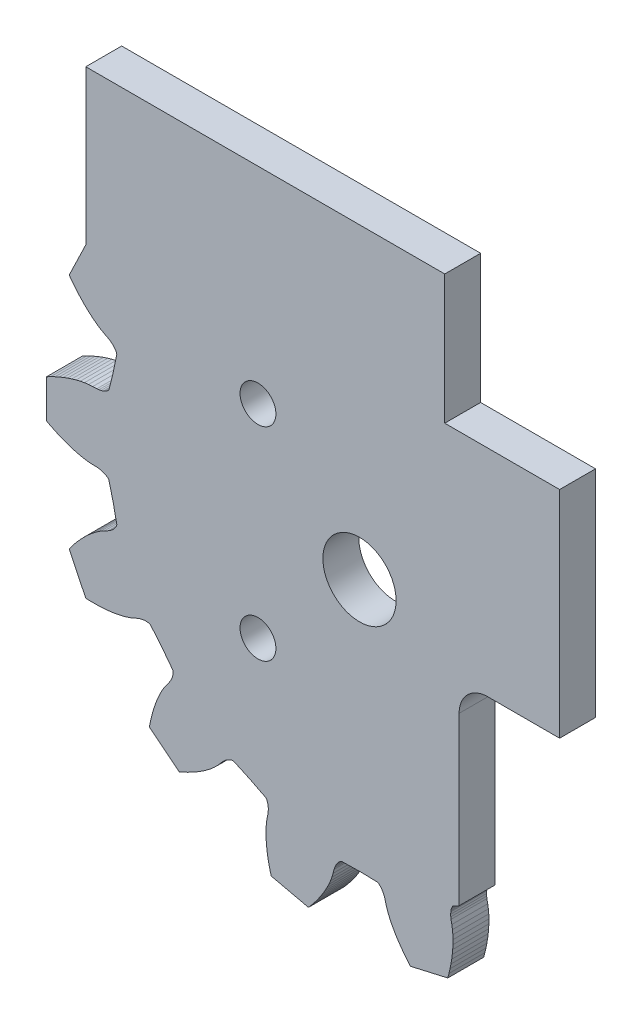
SolidWorks part; units mm, degrees
ref_plane "Front Plane" through (0, 0, 0) normal (0, 0, 1) x (1, 0, 0)
ref_plane "Top Plane" through (0, 0, 0) normal (0, 1, 0) x (1, 0, 0)
ref_plane "Right Plane" through (0, 0, 0) normal (1, 0, 0) x (0, 0, -1)
sketch "Sketch1" plane through (0, 0, 0) normal (0, 0, 1) x (1, 0, 0)
  line L0 (49.5201, 32.7081) -> (49.9074, 31.1602)
  line L1 (49.9074, 31.1602) -> (50.0141, 31.0551)
  line L2 (50.0141, 31.0551) -> (50.1157, 30.9819)
  line L3 (50.1157, 30.9819) -> (50.2145, 30.9258)
  line L4 (50.2145, 30.9258) -> (50.3116, 30.8811)
  line L5 (50.3116, 30.8811) -> (50.4073, 30.845)
  line L6 (50.4073, 30.845) -> (50.596, 30.7914)
  line L7 (50.596, 30.7914) -> (50.782, 30.7566)
  line L8 (50.782, 30.7566) -> (50.9659, 30.736)
  line L9 (50.9659, 30.736) -> (51.3296, 30.7264)
  line L10 (51.3296, 30.7264) -> (51.6946, 30.7028)
  line L11 (51.6946, 30.7028) -> (52.0629, 30.6532)
  line L12 (52.0629, 30.6532) -> (52.4332, 30.5824)
  line L13 (52.4332, 30.5824) -> (52.8051, 30.4927)
  line L14 (52.8051, 30.4927) -> (53.1779, 30.3858)
  line L15 (53.1779, 30.3858) -> (53.5516, 30.2626)
  line L16 (53.5516, 30.2626) -> (53.9257, 30.1241)
  line L17 (53.9257, 30.1241) -> (54.3001, 29.9707)
  line L18 (54.3001, 29.9707) -> (54.6743, 29.8031)
  line L19 (54.6743, 29.8031) -> (55.0479, 29.6212)
  line L20 (55.0479, 29.6212) -> (55.4208, 29.4262)
  line L21 (55.4208, 29.4262) -> (55.4208, 26.0462)
  line L22 (55.4208, 26.0462) -> (55.0479, 25.8511)
  line L23 (55.0479, 25.8511) -> (54.6743, 25.6692)
  line L24 (54.6743, 25.6692) -> (54.3001, 25.5016)
  line L25 (54.3001, 25.5016) -> (53.9257, 25.3482)
  line L26 (53.9257, 25.3482) -> (53.5516, 25.2098)
  line L27 (53.5516, 25.2098) -> (53.1779, 25.0866)
  line L28 (53.1779, 25.0866) -> (52.8051, 24.9796)
  line L29 (52.8051, 24.9796) -> (52.4332, 24.89)
  line L30 (52.4332, 24.89) -> (52.0629, 24.8191)
  line L31 (52.0629, 24.8191) -> (51.6946, 24.7693)
  line L32 (51.6946, 24.7693) -> (51.3296, 24.746)
  line L33 (51.3296, 24.746) -> (50.9659, 24.7363)
  line L34 (50.9659, 24.7363) -> (50.782, 24.7157)
  line L35 (50.782, 24.7157) -> (50.596, 24.6809)
  line L36 (50.596, 24.6809) -> (50.4073, 24.6273)
  line L37 (50.4073, 24.6273) -> (50.3116, 24.5913)
  line L38 (50.3116, 24.5913) -> (50.2145, 24.5466)
  line L39 (50.2145, 24.5466) -> (50.1157, 24.4904)
  line L40 (50.1157, 24.4904) -> (50.0141, 24.4173)
  line L41 (50.0141, 24.4173) -> (49.9074, 24.3121)
  line L42 (49.9074, 24.3121) -> (49.5201, 22.7642)
  line L43 (49.5201, 22.7642) -> (49.1973, 21.2014)
  line L44 (49.1973, 21.2014) -> (49.2481, 21.0604)
  line L45 (49.2481, 21.0604) -> (49.3077, 20.9502)
  line L46 (49.3077, 20.9502) -> (49.3725, 20.857)
  line L47 (49.3725, 20.857) -> (49.4406, 20.7747)
  line L48 (49.4406, 20.7747) -> (49.511, 20.7005)
  line L49 (49.511, 20.7005) -> (49.6578, 20.5702)
  line L50 (49.6578, 20.5702) -> (49.8102, 20.4582)
  line L51 (49.8102, 20.4582) -> (49.9669, 20.3601)
  line L52 (49.9669, 20.3601) -> (50.2905, 20.1935)
  line L53 (50.2905, 20.1935) -> (50.6092, 20.0139)
  line L54 (50.6092, 20.0139) -> (50.9194, 19.8095)
  line L55 (50.9194, 19.8095) -> (51.2224, 19.5849)
  line L56 (51.2224, 19.5849) -> (51.5183, 19.3429)
  line L57 (51.5183, 19.3429) -> (51.8081, 19.0845)
  line L58 (51.8081, 19.0845) -> (52.0913, 18.8115)
  line L59 (52.0913, 18.8115) -> (52.3682, 18.5242)
  line L60 (52.3682, 18.5242) -> (52.639, 18.2237)
  line L61 (52.639, 18.2237) -> (52.9034, 17.9103)
  line L62 (52.9034, 17.9103) -> (53.1612, 17.5844)
  line L63 (53.1612, 17.5844) -> (53.4124, 17.2469)
  line L64 (53.4124, 17.2469) -> (51.946, 14.2016)
  line L65 (51.946, 14.2016) -> (51.5252, 14.1877)
  line L66 (51.5252, 14.1877) -> (51.1099, 14.1862)
  line L67 (51.1099, 14.1862) -> (50.6999, 14.1973)
  line L68 (50.6999, 14.1973) -> (50.2961, 14.2215)
  line L69 (50.2961, 14.2215) -> (49.8991, 14.2591)
  line L70 (49.8991, 14.2591) -> (49.5089, 14.3101)
  line L71 (49.5089, 14.3101) -> (49.1264, 14.3756)
  line L72 (49.1264, 14.3756) -> (48.7525, 14.4562)
  line L73 (48.7525, 14.4562) -> (48.388, 14.5529)
  line L74 (48.388, 14.5529) -> (48.035, 14.668)
  line L75 (48.035, 14.668) -> (47.6956, 14.8054)
  line L76 (47.6956, 14.8054) -> (47.3636, 14.9542)
  line L77 (47.3636, 14.9542) -> (47.1891, 15.0157)
  line L78 (47.1891, 15.0157) -> (47.0065, 15.065)
  line L79 (47.0065, 15.065) -> (46.8135, 15.0985)
  line L80 (46.8135, 15.0985) -> (46.7114, 15.1074)
  line L81 (46.7114, 15.1074) -> (46.6047, 15.1094)
  line L82 (46.6047, 15.1094) -> (46.4914, 15.1018)
  line L83 (46.4914, 15.1018) -> (46.368, 15.0797)
  line L84 (46.368, 15.0797) -> (46.226, 15.0315)
  line L85 (46.226, 15.0315) -> (45.2056, 13.8049)
  line L86 (45.2056, 13.8049) -> (44.2366, 12.5369)
  line L87 (44.2366, 12.5369) -> (44.2211, 12.3878)
  line L88 (44.2211, 12.3878) -> (44.2272, 12.2626)
  line L89 (44.2272, 12.2626) -> (44.245, 12.1506)
  line L90 (44.245, 12.1506) -> (44.2707, 12.0467)
  line L91 (44.2707, 12.0467) -> (44.3019, 11.9494)
  line L92 (44.3019, 11.9494) -> (44.3776, 11.7686)
  line L93 (44.3776, 11.7686) -> (44.4663, 11.6014)
  line L94 (44.4663, 11.6014) -> (44.5651, 11.445)
  line L95 (44.5651, 11.445) -> (44.784, 11.1544)
  line L96 (44.784, 11.1544) -> (44.9936, 10.8544)
  line L97 (44.9936, 10.8544) -> (45.1843, 10.5357)
  line L98 (45.1843, 10.5357) -> (45.3598, 10.2019)
  line L99 (45.3598, 10.2019) -> (45.5214, 9.8552)
  line L100 (45.5214, 9.8552) -> (45.6705, 9.4971)
  line L101 (45.6705, 9.4971) -> (45.8071, 9.128)
  line L102 (45.8071, 9.128) -> (45.9321, 8.749)
  line L103 (45.9321, 8.749) -> (46.0456, 8.3609)
  line L104 (46.0456, 8.3609) -> (46.1477, 7.9637)
  line L105 (46.1477, 7.9637) -> (46.2387, 7.5583)
  line L106 (46.2387, 7.5583) -> (46.3184, 7.145)
  line L107 (46.3184, 7.145) -> (43.6761, 5.0378)
  line L108 (43.6761, 5.0378) -> (43.2907, 5.2075)
  line L109 (43.2907, 5.2075) -> (42.9158, 5.3866)
  line L110 (42.9158, 5.3866) -> (42.5516, 5.5745)
  line L111 (42.5516, 5.5745) -> (42.1983, 5.7714)
  line L112 (42.1983, 5.7714) -> (41.8567, 5.9776)
  line L113 (41.8567, 5.9776) -> (41.5272, 6.193)
  line L114 (41.5272, 6.193) -> (41.2112, 6.4178)
  line L115 (41.2112, 6.4178) -> (40.9092, 6.6528)
  line L116 (40.9092, 6.6528) -> (40.623, 6.8979)
  line L117 (40.623, 6.8979) -> (40.3545, 7.1549)
  line L118 (40.3545, 7.1549) -> (40.1086, 7.4259)
  line L119 (40.1086, 7.4259) -> (39.8742, 7.7041)
  line L120 (39.8742, 7.7041) -> (39.7436, 7.8351)
  line L121 (39.7436, 7.8351) -> (39.6004, 7.9588)
  line L122 (39.6004, 7.9588) -> (39.4409, 8.0729)
  line L123 (39.4409, 8.0729) -> (39.353, 8.125)
  line L124 (39.353, 8.125) -> (39.2575, 8.1732)
  line L125 (39.2575, 8.1732) -> (39.1521, 8.2154)
  line L126 (39.1521, 8.2154) -> (39.0314, 8.2492)
  line L127 (39.0314, 8.2492) -> (38.8826, 8.2672)
  line L128 (38.8826, 8.2672) -> (37.431, 7.6048)
  line L129 (37.431, 7.6048) -> (36.0081, 6.8829)
  line L130 (36.0081, 6.8829) -> (35.9293, 6.7551)
  line L131 (35.9293, 6.7551) -> (35.8803, 6.6398)
  line L132 (35.8803, 6.6398) -> (35.8478, 6.5311)
  line L133 (35.8478, 6.5311) -> (35.8257, 6.4265)
  line L134 (35.8257, 6.4265) -> (35.8117, 6.3251)
  line L135 (35.8117, 6.3251) -> (35.8016, 6.1293)
  line L136 (35.8016, 6.1293) -> (35.8089, 5.9403)
  line L137 (35.8089, 5.9403) -> (35.83, 5.7564)
  line L138 (35.83, 5.7564) -> (35.9014, 5.3998)
  line L139 (35.9014, 5.3998) -> (35.9598, 5.0386)
  line L140 (35.9598, 5.0386) -> (35.9933, 4.6685)
  line L141 (35.9933, 4.6685) -> (36.0065, 4.2918)
  line L142 (36.0065, 4.2918) -> (36.002, 3.9093)
  line L143 (36.002, 3.9093) -> (35.9806, 3.522)
  line L144 (35.9806, 3.522) -> (35.9438, 3.13)
  line L145 (35.9438, 3.13) -> (35.892, 2.7346)
  line L146 (35.892, 2.7346) -> (35.8257, 2.3355)
  line L147 (35.8257, 2.3355) -> (35.7454, 1.9334)
  line L148 (35.7454, 1.9334) -> (35.6514, 1.5288)
  line L149 (35.6514, 1.5288) -> (35.544, 1.1217)
  line L150 (35.544, 1.1217) -> (32.2491, 0.3696)
  line L151 (32.2491, 0.3696) -> (31.9758, 0.6896)
  line L152 (31.9758, 0.6896) -> (31.7155, 1.0137)
  line L153 (31.7155, 1.0137) -> (31.4688, 1.3411)
  line L154 (31.4688, 1.3411) -> (31.2359, 1.6718)
  line L155 (31.2359, 1.6718) -> (31.0175, 2.0058)
  line L156 (31.0175, 2.0058) -> (30.8143, 2.3426)
  line L157 (30.8143, 2.3426) -> (30.6271, 2.6825)
  line L158 (30.6271, 2.6825) -> (30.4569, 3.0251)
  line L159 (30.4569, 3.0251) -> (30.3055, 3.3703)
  line L160 (30.3055, 3.3703) -> (30.1752, 3.7181)
  line L161 (30.1752, 3.7181) -> (30.0711, 4.0691)
  line L162 (30.0711, 4.0691) -> (29.9806, 4.4214)
  line L163 (29.9806, 4.4214) -> (29.9197, 4.5961)
  line L164 (29.9197, 4.5961) -> (29.8445, 4.7696)
  line L165 (29.8445, 4.7696) -> (29.7503, 4.9416)
  line L166 (29.7503, 4.9416) -> (29.6936, 5.0269)
  line L167 (29.6936, 5.0269) -> (29.6283, 5.1115)
  line L168 (29.6283, 5.1115) -> (29.5519, 5.1953)
  line L169 (29.5519, 5.1953) -> (29.4577, 5.2781)
  line L170 (29.4577, 5.2781) -> (29.3314, 5.3589)
  line L171 (29.3314, 5.3589) -> (27.736, 5.3919)
  line L172 (27.736, 5.3919) -> (26.1409, 5.3589)
  line L173 (26.1409, 5.3589) -> (26.0147, 5.2781)
  line L174 (26.0147, 5.2781) -> (25.9204, 5.1953)
  line L175 (25.9204, 5.1953) -> (25.8437, 5.1115)
  line L176 (25.8437, 5.1115) -> (25.7787, 5.0269)
  line L177 (25.7787, 5.0269) -> (25.7221, 4.9416)
  line L178 (25.7221, 4.9416) -> (25.6278, 4.7696)
  line L179 (25.6278, 4.7696) -> (25.5527, 4.5961)
  line L180 (25.5527, 4.5961) -> (25.4917, 4.4214)
  line L181 (25.4917, 4.4214) -> (25.4013, 4.0691)
  line L182 (25.4013, 4.0691) -> (25.2971, 3.7181)
  line L183 (25.2971, 3.7181) -> (25.1668, 3.3703)
  line L184 (25.1668, 3.3703) -> (25.0154, 3.0251)
  line L185 (25.0154, 3.0251) -> (24.8453, 2.6825)
  line L186 (24.8453, 2.6825) -> (24.6581, 2.3426)
  line L187 (24.6581, 2.3426) -> (24.4549, 2.0058)
  line L188 (24.4549, 2.0058) -> (24.2364, 1.6718)
  line L189 (24.2364, 1.6718) -> (24.0035, 1.3411)
  line L190 (24.0035, 1.3411) -> (23.7569, 1.0137)
  line L191 (23.7569, 1.0137) -> (23.4965, 0.6896)
  line L192 (23.4965, 0.6896) -> (23.2232, 0.3696)
  line L193 (23.2232, 0.3696) -> (19.9283, 1.1217)
  line L194 (19.9283, 1.1217) -> (19.8209, 1.5288)
  line L195 (19.8209, 1.5288) -> (19.7269, 1.9334)
  line L196 (19.7269, 1.9334) -> (19.6466, 2.3355)
  line L197 (19.6466, 2.3355) -> (19.5804, 2.7346)
  line L198 (19.5804, 2.7346) -> (19.5285, 3.13)
  line L199 (19.5285, 3.13) -> (19.4917, 3.522)
  line L200 (19.4917, 3.522) -> (19.4704, 3.9093)
  line L201 (19.4704, 3.9093) -> (19.4658, 4.2918)
  line L202 (19.4658, 4.2918) -> (19.479, 4.6685)
  line L203 (19.479, 4.6685) -> (19.5125, 5.0386)
  line L204 (19.5125, 5.0386) -> (19.571, 5.3998)
  line L205 (19.571, 5.3998) -> (19.6423, 5.7564)
  line L206 (19.6423, 5.7564) -> (19.6634, 5.9403)
  line L207 (19.6634, 5.9403) -> (19.6708, 6.1293)
  line L208 (19.6708, 6.1293) -> (19.6606, 6.3251)
  line L209 (19.6606, 6.3251) -> (19.6466, 6.4265)
  line L210 (19.6466, 6.4265) -> (19.6245, 6.5311)
  line L211 (19.6245, 6.5311) -> (19.592, 6.6398)
  line L212 (19.592, 6.6398) -> (19.543, 6.7551)
  line L213 (19.543, 6.7551) -> (19.4643, 6.8829)
  line L214 (19.4643, 6.8829) -> (18.0414, 7.6048)
  line L215 (18.0414, 7.6048) -> (16.5898, 8.2672)
  line L216 (16.5898, 8.2672) -> (16.4409, 8.2492)
  line L217 (16.4409, 8.2492) -> (16.3203, 8.2154)
  line L218 (16.3203, 8.2154) -> (16.2149, 8.1732)
  line L219 (16.2149, 8.1732) -> (16.1193, 8.125)
  line L220 (16.1193, 8.125) -> (16.0315, 8.0729)
  line L221 (16.0315, 8.0729) -> (15.872, 7.9588)
  line L222 (15.872, 7.9588) -> (15.7287, 7.8351)
  line L223 (15.7287, 7.8351) -> (15.5981, 7.7041)
  line L224 (15.5981, 7.7041) -> (15.3637, 7.4259)
  line L225 (15.3637, 7.4259) -> (15.1178, 7.1549)
  line L226 (15.1178, 7.1549) -> (14.8493, 6.8979)
  line L227 (14.8493, 6.8979) -> (14.5631, 6.6528)
  line L228 (14.5631, 6.6528) -> (14.2611, 6.4178)
  line L229 (14.2611, 6.4178) -> (13.9451, 6.193)
  line L230 (13.9451, 6.193) -> (13.6157, 5.9776)
  line L231 (13.6157, 5.9776) -> (13.274, 5.7714)
  line L232 (13.274, 5.7714) -> (12.9207, 5.5745)
  line L233 (12.9207, 5.5745) -> (12.5565, 5.3866)
  line L234 (12.5565, 5.3866) -> (12.1816, 5.2075)
  line L235 (12.1816, 5.2075) -> (11.7963, 5.0378)
  line L236 (11.7963, 5.0378) -> (9.1539, 7.145)
  line L237 (9.1539, 7.145) -> (9.2337, 7.5583)
  line L238 (9.2337, 7.5583) -> (9.3246, 7.9637)
  line L239 (9.3246, 7.9637) -> (9.4267, 8.3609)
  line L240 (9.4267, 8.3609) -> (9.5402, 8.749)
  line L241 (9.5402, 8.749) -> (9.6652, 9.128)
  line L242 (9.6652, 9.128) -> (9.8019, 9.4971)
  line L243 (9.8019, 9.4971) -> (9.951, 9.8552)
  line L244 (9.951, 9.8552) -> (10.1125, 10.2019)
  line L245 (10.1125, 10.2019) -> (10.288, 10.5357)
  line L246 (10.288, 10.5357) -> (10.4788, 10.8544)
  line L247 (10.4788, 10.8544) -> (10.6883, 11.1544)
  line L248 (10.6883, 11.1544) -> (10.9073, 11.445)
  line L249 (10.9073, 11.445) -> (11.0058, 11.6014)
  line L250 (11.0058, 11.6014) -> (11.0947, 11.7686)
  line L251 (11.0947, 11.7686) -> (11.1704, 11.9494)
  line L252 (11.1704, 11.9494) -> (11.2017, 12.0467)
  line L253 (11.2017, 12.0467) -> (11.2273, 12.1506)
  line L254 (11.2273, 12.1506) -> (11.2451, 12.2626)
  line L255 (11.2451, 12.2626) -> (11.2512, 12.3878)
  line L256 (11.2512, 12.3878) -> (11.2354, 12.5369)
  line L257 (11.2354, 12.5369) -> (10.2667, 13.8049)
  line L258 (10.2667, 13.8049) -> (9.2464, 15.0315)
  line L259 (9.2464, 15.0315) -> (9.1044, 15.0797)
  line L260 (9.1044, 15.0797) -> (8.9809, 15.1018)
  line L261 (8.9809, 15.1018) -> (8.8676, 15.1094)
  line L262 (8.8676, 15.1094) -> (8.761, 15.1074)
  line L263 (8.761, 15.1074) -> (8.6589, 15.0985)
  line L264 (8.6589, 15.0985) -> (8.4658, 15.065)
  line L265 (8.4658, 15.065) -> (8.2832, 15.0157)
  line L266 (8.2832, 15.0157) -> (8.1087, 14.9542)
  line L267 (8.1087, 14.9542) -> (7.7767, 14.8054)
  line L268 (7.7767, 14.8054) -> (7.4374, 14.668)
  line L269 (7.4374, 14.668) -> (7.0843, 14.5529)
  line L270 (7.0843, 14.5529) -> (6.7198, 14.4562)
  line L271 (6.7198, 14.4562) -> (6.3459, 14.3756)
  line L272 (6.3459, 14.3756) -> (5.9634, 14.3101)
  line L273 (5.9634, 14.3101) -> (5.5733, 14.2591)
  line L274 (5.5733, 14.2591) -> (5.1763, 14.2215)
  line L275 (5.1763, 14.2215) -> (4.7724, 14.1973)
  line L276 (4.7724, 14.1973) -> (4.3624, 14.1862)
  line L277 (4.3624, 14.1862) -> (3.9472, 14.1877)
  line L278 (3.9472, 14.1877) -> (3.5263, 14.2016)
  line L279 (3.5263, 14.2016) -> (2.0599, 17.2469)
  line L280 (2.0599, 17.2469) -> (2.3111, 17.5844)
  line L281 (2.3111, 17.5844) -> (2.569, 17.9103)
  line L282 (2.569, 17.9103) -> (2.8334, 18.2237)
  line L283 (2.8334, 18.2237) -> (3.1041, 18.5242)
  line L284 (3.1041, 18.5242) -> (3.381, 18.8115)
  line L285 (3.381, 18.8115) -> (3.6642, 19.0845)
  line L286 (3.6642, 19.0845) -> (3.954, 19.3429)
  line L287 (3.954, 19.3429) -> (4.2499, 19.5849)
  line L288 (4.2499, 19.5849) -> (4.553, 19.8095)
  line L289 (4.553, 19.8095) -> (4.8631, 20.0139)
  line L290 (4.8631, 20.0139) -> (5.1819, 20.1935)
  line L291 (5.1819, 20.1935) -> (5.5054, 20.3601)
  line L292 (5.5054, 20.3601) -> (5.6622, 20.4582)
  line L293 (5.6622, 20.4582) -> (5.8146, 20.5702)
  line L294 (5.8146, 20.5702) -> (5.9614, 20.7005)
  line L295 (5.9614, 20.7005) -> (6.0317, 20.7747)
  line L296 (6.0317, 20.7747) -> (6.0998, 20.857)
  line L297 (6.0998, 20.857) -> (6.1646, 20.9502)
  line L298 (6.1646, 20.9502) -> (6.2243, 21.0604)
  line L299 (6.2243, 21.0604) -> (6.2748, 21.2014)
  line L300 (6.2748, 21.2014) -> (5.9522, 22.7642)
  line L301 (5.9522, 22.7642) -> (5.5649, 24.3121)
  line L302 (5.5649, 24.3121) -> (5.4582, 24.4173)
  line L303 (5.4582, 24.4173) -> (5.3566, 24.4904)
  line L304 (5.3566, 24.4904) -> (5.2578, 24.5466)
  line L305 (5.2578, 24.5466) -> (5.1608, 24.5913)
  line L306 (5.1608, 24.5913) -> (5.065, 24.6273)
  line L307 (5.065, 24.6273) -> (4.8763, 24.6809)
  line L308 (4.8763, 24.6809) -> (4.6904, 24.7157)
  line L309 (4.6904, 24.7157) -> (4.5065, 24.7363)
  line L310 (4.5065, 24.7363) -> (4.1427, 24.746)
  line L311 (4.1427, 24.746) -> (3.7777, 24.7693)
  line L312 (3.7777, 24.7693) -> (3.4094, 24.8191)
  line L313 (3.4094, 24.8191) -> (3.0391, 24.89)
  line L314 (3.0391, 24.89) -> (2.6673, 24.9796)
  line L315 (2.6673, 24.9796) -> (2.2944, 25.0866)
  line L316 (2.2944, 25.0866) -> (1.9207, 25.2098)
  line L317 (1.9207, 25.2098) -> (1.5466, 25.3482)
  line L318 (1.5466, 25.3482) -> (1.1722, 25.5016)
  line L319 (1.1722, 25.5016) -> (0.7981, 25.6692)
  line L320 (0.7981, 25.6692) -> (0.4244, 25.8511)
  line L321 (0.4244, 25.8511) -> (0.0516, 26.0462)
  line L322 (0.0516, 26.0462) -> (0.0516, 29.4262)
  line L323 (0.0516, 29.4262) -> (0.4244, 29.6212)
  line L324 (0.4244, 29.6212) -> (0.7981, 29.8031)
  line L325 (0.7981, 29.8031) -> (1.1722, 29.9707)
  line L326 (1.1722, 29.9707) -> (1.5466, 30.1241)
  line L327 (1.5466, 30.1241) -> (1.9207, 30.2626)
  line L328 (1.9207, 30.2626) -> (2.2944, 30.3858)
  line L329 (2.2944, 30.3858) -> (2.6673, 30.4927)
  line L330 (2.6673, 30.4927) -> (3.0391, 30.5824)
  line L331 (3.0391, 30.5824) -> (3.4094, 30.6532)
  line L332 (3.4094, 30.6532) -> (3.7777, 30.7028)
  line L333 (3.7777, 30.7028) -> (4.1427, 30.7264)
  line L334 (4.1427, 30.7264) -> (4.5065, 30.736)
  line L335 (4.5065, 30.736) -> (4.6904, 30.7566)
  line L336 (4.6904, 30.7566) -> (4.8763, 30.7914)
  line L337 (4.8763, 30.7914) -> (5.065, 30.845)
  line L338 (5.065, 30.845) -> (5.1608, 30.8811)
  line L339 (5.1608, 30.8811) -> (5.2578, 30.9258)
  line L340 (5.2578, 30.9258) -> (5.3566, 30.9819)
  line L341 (5.3566, 30.9819) -> (5.4582, 31.0551)
  line L342 (5.4582, 31.0551) -> (5.5649, 31.1602)
  line L343 (5.5649, 31.1602) -> (5.9522, 32.7081)
  line L344 (5.9522, 32.7081) -> (6.2748, 34.2709)
  line L345 (6.2748, 34.2709) -> (6.2243, 34.4119)
  line L346 (6.2243, 34.4119) -> (6.1646, 34.5222)
  line L347 (6.1646, 34.5222) -> (6.0998, 34.6154)
  line L348 (6.0998, 34.6154) -> (6.0317, 34.6977)
  line L349 (6.0317, 34.6977) -> (5.9614, 34.7718)
  line L350 (5.9614, 34.7718) -> (5.8146, 34.9021)
  line L351 (5.8146, 34.9021) -> (5.6622, 35.0142)
  line L352 (5.6622, 35.0142) -> (5.5054, 35.1122)
  line L353 (5.5054, 35.1122) -> (5.1819, 35.2788)
  line L354 (5.1819, 35.2788) -> (4.8631, 35.4584)
  line L355 (4.8631, 35.4584) -> (4.553, 35.6629)
  line L356 (4.553, 35.6629) -> (4.2499, 35.8874)
  line L357 (4.2499, 35.8874) -> (3.954, 36.1295)
  line L358 (3.954, 36.1295) -> (3.6642, 36.3878)
  line L359 (3.6642, 36.3878) -> (3.381, 36.6608)
  line L360 (3.381, 36.6608) -> (3.1041, 36.9481)
  line L361 (3.1041, 36.9481) -> (2.8334, 37.2486)
  line L362 (2.8334, 37.2486) -> (2.569, 37.562)
  line L363 (2.569, 37.562) -> (2.3111, 37.8879)
  line L364 (2.3111, 37.8879) -> (2.0599, 38.2255)
  line L365 (2.0599, 38.2255) -> (3.5263, 41.2707)
  line L366 (3.5263, 41.2707) -> (3.9472, 41.2847)
  line L367 (3.9472, 41.2847) -> (4.3624, 41.2862)
  line L368 (4.3624, 41.2862) -> (4.7724, 41.275)
  line L369 (4.7724, 41.275) -> (5.1763, 41.2509)
  line L370 (5.1763, 41.2509) -> (5.5733, 41.2133)
  line L371 (5.5733, 41.2133) -> (5.9634, 41.1622)
  line L372 (5.9634, 41.1622) -> (6.3459, 41.0967)
  line L373 (6.3459, 41.0967) -> (6.7198, 41.0162)
  line L374 (6.7198, 41.0162) -> (7.0843, 40.9194)
  line L375 (7.0843, 40.9194) -> (7.4374, 40.8043)
  line L376 (7.4374, 40.8043) -> (7.7767, 40.6669)
  line L377 (7.7767, 40.6669) -> (8.1087, 40.5181)
  line L378 (8.1087, 40.5181) -> (8.2832, 40.4566)
  line L379 (8.2832, 40.4566) -> (8.4658, 40.4073)
  line L380 (8.4658, 40.4073) -> (8.6589, 40.3738)
  line L381 (8.6589, 40.3738) -> (8.761, 40.3649)
  line L382 (8.761, 40.3649) -> (8.8676, 40.3629)
  line L383 (8.8676, 40.3629) -> (8.9809, 40.3705)
  line L384 (8.9809, 40.3705) -> (9.1044, 40.3926)
  line L385 (9.1044, 40.3926) -> (9.2464, 40.4409)
  line L386 (9.2464, 40.4409) -> (10.2667, 41.6674)
  line L387 (10.2667, 41.6674) -> (11.2354, 42.9354)
  line L388 (11.2354, 42.9354) -> (11.2512, 43.0845)
  line L389 (11.2512, 43.0845) -> (11.2451, 43.2097)
  line L390 (11.2451, 43.2097) -> (11.2273, 43.3217)
  line L391 (11.2273, 43.3217) -> (11.2017, 43.4256)
  line L392 (11.2017, 43.4256) -> (11.1704, 43.5229)
  line L393 (11.1704, 43.5229) -> (11.0947, 43.7037)
  line L394 (11.0947, 43.7037) -> (11.0058, 43.8709)
  line L395 (11.0058, 43.8709) -> (10.9073, 44.0273)
  line L396 (10.9073, 44.0273) -> (10.6883, 44.3179)
  line L397 (10.6883, 44.3179) -> (10.4788, 44.6179)
  line L398 (10.4788, 44.6179) -> (10.288, 44.9367)
  line L399 (10.288, 44.9367) -> (10.1125, 45.2704)
  line L400 (10.1125, 45.2704) -> (9.951, 45.6171)
  line L401 (9.951, 45.6171) -> (9.8019, 45.9753)
  line L402 (9.8019, 45.9753) -> (9.6652, 46.3443)
  line L403 (9.6652, 46.3443) -> (9.5402, 46.7233)
  line L404 (9.5402, 46.7233) -> (9.4267, 47.1114)
  line L405 (9.4267, 47.1114) -> (9.3246, 47.5087)
  line L406 (9.3246, 47.5087) -> (9.2337, 47.9141)
  line L407 (9.2337, 47.9141) -> (9.1539, 48.3273)
  line L408 (9.1539, 48.3273) -> (11.7963, 50.4345)
  line L409 (11.7963, 50.4345) -> (12.1816, 50.2648)
  line L410 (12.1816, 50.2648) -> (12.5565, 50.0858)
  line L411 (12.5565, 50.0858) -> (12.9207, 49.8978)
  line L412 (12.9207, 49.8978) -> (13.274, 49.7009)
  line L413 (13.274, 49.7009) -> (13.6157, 49.4947)
  line L414 (13.6157, 49.4947) -> (13.9451, 49.2793)
  line L415 (13.9451, 49.2793) -> (14.2611, 49.0545)
  line L416 (14.2611, 49.0545) -> (14.5631, 48.8196)
  line L417 (14.5631, 48.8196) -> (14.8493, 48.5745)
  line L418 (14.8493, 48.5745) -> (15.1178, 48.3174)
  line L419 (15.1178, 48.3174) -> (15.3637, 48.0464)
  line L420 (15.3637, 48.0464) -> (15.5981, 47.7683)
  line L421 (15.5981, 47.7683) -> (15.7287, 47.6372)
  line L422 (15.7287, 47.6372) -> (15.872, 47.5135)
  line L423 (15.872, 47.5135) -> (16.0315, 47.3994)
  line L424 (16.0315, 47.3994) -> (16.1193, 47.3471)
  line L425 (16.1193, 47.3471) -> (16.2149, 47.2991)
  line L426 (16.2149, 47.2991) -> (16.3203, 47.257)
  line L427 (16.3203, 47.257) -> (16.4409, 47.2232)
  line L428 (16.4409, 47.2232) -> (16.5898, 47.2051)
  line L429 (16.5898, 47.2051) -> (18.0414, 47.8676)
  line L430 (18.0414, 47.8676) -> (19.4643, 48.5894)
  line L431 (19.4643, 48.5894) -> (19.543, 48.7172)
  line L432 (19.543, 48.7172) -> (19.592, 48.8325)
  line L433 (19.592, 48.8325) -> (19.6245, 48.9412)
  line L434 (19.6245, 48.9412) -> (19.6466, 49.0459)
  line L435 (19.6466, 49.0459) -> (19.6606, 49.1472)
  line L436 (19.6606, 49.1472) -> (19.6708, 49.3431)
  line L437 (19.6708, 49.3431) -> (19.6634, 49.532)
  line L438 (19.6634, 49.532) -> (19.6423, 49.7159)
  line L439 (19.6423, 49.7159) -> (19.571, 50.0725)
  line L440 (19.571, 50.0725) -> (19.5125, 50.4337)
  line L441 (19.5125, 50.4337) -> (19.479, 50.8038)
  line L442 (19.479, 50.8038) -> (19.4658, 51.1805)
  line L443 (19.4658, 51.1805) -> (19.4704, 51.563)
  line L444 (19.4704, 51.563) -> (19.4917, 51.9504)
  line L445 (19.4917, 51.9504) -> (19.5285, 52.3423)
  line L446 (19.5285, 52.3423) -> (19.5804, 52.7378)
  line L447 (19.5804, 52.7378) -> (19.8209, 52.7378)
  line L448 (19.8209, 52.7378) -> (20.3725, 53.1297)
  line L449 (20.3725, 53.1297) -> (21.0344, 53.4665)
  line L450 (21.0344, 53.4665) -> (21.4927, 53.8005)
  line L451 (21.4927, 53.8005) -> (22.3582, 54.1312)
  line L452 (22.3582, 54.1312) -> (23.2232, 54.1312)
  line L453 (23.2232, 54.1312) -> (23.7569, 54.1312)
  line L454 (23.7569, 54.1312) -> (24.0035, 54.1312)
  line L455 (24.0035, 54.1312) -> (24.2364, 53.8005)
  line L456 (24.2364, 53.8005) -> (24.4549, 53.4665)
  line L457 (24.4549, 53.4665) -> (24.6581, 53.1297)
  line L458 (24.6581, 53.1297) -> (24.8453, 52.7898)
  line L459 (24.8453, 52.7898) -> (25.0154, 52.4472)
  line L460 (25.0154, 52.4472) -> (25.1668, 52.102)
  line L461 (25.1668, 52.102) -> (25.2971, 51.754)
  line L462 (25.2971, 51.754) -> (25.4013, 51.4033)
  line L463 (25.4013, 51.4033) -> (25.4917, 51.051)
  line L464 (25.4917, 51.051) -> (25.5527, 50.8762)
  line L465 (25.5527, 50.8762) -> (25.6278, 50.7027)
  line L466 (25.6278, 50.7027) -> (25.7221, 50.5308)
  line L467 (25.7221, 50.5308) -> (25.7787, 50.4454)
  line L468 (25.7787, 50.4454) -> (25.8437, 50.3608)
  line L469 (25.8437, 50.3608) -> (25.9204, 50.277)
  line L470 (25.9204, 50.277) -> (26.0147, 50.1942)
  line L471 (26.0147, 50.1942) -> (26.1409, 50.1134)
  line L472 (26.1409, 50.1134) -> (27.736, 50.0804)
  line L473 (27.736, 50.0804) -> (29.3314, 50.1134)
  line L474 (29.3314, 50.1134) -> (29.4577, 50.1942)
  line L475 (29.4577, 50.1942) -> (29.5519, 50.277)
  line L476 (29.5519, 50.277) -> (29.6283, 50.3608)
  line L477 (29.6283, 50.3608) -> (29.6936, 50.4454)
  line L478 (29.6936, 50.4454) -> (29.7503, 50.5308)
  line L479 (29.7503, 50.5308) -> (29.8445, 50.7027)
  line L480 (29.8445, 50.7027) -> (29.9197, 50.8762)
  line L481 (29.9197, 50.8762) -> (29.9806, 51.051)
  line L482 (29.9806, 51.051) -> (30.0711, 51.4033)
  line L483 (30.0711, 51.4033) -> (30.1752, 51.754)
  line L484 (30.1752, 51.754) -> (30.3055, 52.102)
  line L485 (30.3055, 52.102) -> (30.4569, 52.4472)
  line L486 (30.4569, 52.4472) -> (30.6271, 52.7898)
  line L487 (30.6271, 52.7898) -> (30.8143, 53.1297)
  line L488 (30.8143, 53.1297) -> (31.0175, 53.4665)
  line L489 (31.0175, 53.4665) -> (31.2359, 53.8005)
  line L490 (31.2359, 53.8005) -> (31.4688, 54.1312)
  line L491 (31.4688, 54.1312) -> (31.9758, 53.8005)
  line L492 (31.9758, 53.8005) -> (32.7958, 53.8005)
  line L493 (32.7958, 53.8005) -> (33.7632, 53.8005)
  line L494 (33.7632, 53.8005) -> (34.6287, 53.8005)
  line L495 (34.6287, 53.8005) -> (35.4434, 53.6108)
  line L496 (35.4434, 53.6108) -> (35.7454, 53.5389)
  line L497 (35.7454, 53.5389) -> (35.8257, 53.1368)
  line L498 (35.8257, 53.1368) -> (35.892, 52.7378)
  line L499 (35.892, 52.7378) -> (35.9438, 52.3423)
  line L500 (35.9438, 52.3423) -> (35.9806, 51.9504)
  line L501 (35.9806, 51.9504) -> (36.002, 51.563)
  line L502 (36.002, 51.563) -> (36.0065, 51.1805)
  line L503 (36.0065, 51.1805) -> (35.9933, 50.8038)
  line L504 (35.9933, 50.8038) -> (35.9598, 50.4337)
  line L505 (35.9598, 50.4337) -> (35.9014, 50.0725)
  line L506 (35.9014, 50.0725) -> (35.83, 49.7159)
  line L507 (35.83, 49.7159) -> (35.8089, 49.532)
  line L508 (35.8089, 49.532) -> (35.8016, 49.3431)
  line L509 (35.8016, 49.3431) -> (35.8117, 49.1472)
  line L510 (35.8117, 49.1472) -> (35.8257, 49.0459)
  line L511 (35.8257, 49.0459) -> (35.8478, 48.9412)
  line L512 (35.8478, 48.9412) -> (35.8803, 48.8325)
  line L513 (35.8803, 48.8325) -> (35.9293, 48.7172)
  line L514 (35.9293, 48.7172) -> (36.0081, 48.5894)
  line L515 (36.0081, 48.5894) -> (37.431, 47.8676)
  line L516 (37.431, 47.8676) -> (38.8826, 47.2051)
  line L517 (38.8826, 47.2051) -> (39.0314, 47.2232)
  line L518 (39.0314, 47.2232) -> (39.1521, 47.257)
  line L519 (39.1521, 47.257) -> (39.2575, 47.2991)
  line L520 (39.2575, 47.2991) -> (39.353, 47.3471)
  line L521 (39.353, 47.3471) -> (39.4409, 47.3994)
  line L522 (39.4409, 47.3994) -> (39.6004, 47.5135)
  line L523 (39.6004, 47.5135) -> (39.7436, 47.6372)
  line L524 (39.7436, 47.6372) -> (39.8742, 47.7683)
  line L525 (39.8742, 47.7683) -> (40.1086, 48.0464)
  line L526 (40.1086, 48.0464) -> (40.3545, 48.3174)
  line L527 (40.3545, 48.3174) -> (40.623, 48.5745)
  line L528 (40.623, 48.5745) -> (40.9092, 48.8196)
  line L529 (40.9092, 48.8196) -> (41.2112, 49.0545)
  line L530 (41.2112, 49.0545) -> (41.5272, 49.2793)
  line L531 (41.5272, 49.2793) -> (41.8567, 49.4947)
  line L532 (41.8567, 49.4947) -> (42.1983, 49.7009)
  line L533 (42.1983, 49.7009) -> (42.5516, 49.8978)
  line L534 (42.5516, 49.8978) -> (42.9158, 50.0858)
  line L535 (42.9158, 50.0858) -> (43.2907, 50.2648)
  line L536 (43.2907, 50.2648) -> (43.6761, 50.4345)
  line L537 (43.6761, 50.4345) -> (46.3184, 48.3273)
  line L538 (46.3184, 48.3273) -> (46.2387, 47.9141)
  line L539 (46.2387, 47.9141) -> (46.1477, 47.5087)
  line L540 (46.1477, 47.5087) -> (46.0456, 47.1114)
  line L541 (46.0456, 47.1114) -> (45.9321, 46.7233)
  line L542 (45.9321, 46.7233) -> (45.8071, 46.3443)
  line L543 (45.8071, 46.3443) -> (45.6705, 45.9753)
  line L544 (45.6705, 45.9753) -> (45.5214, 45.6171)
  line L545 (45.5214, 45.6171) -> (45.3598, 45.2704)
  line L546 (45.3598, 45.2704) -> (45.1843, 44.9367)
  line L547 (45.1843, 44.9367) -> (44.9936, 44.6179)
  line L548 (44.9936, 44.6179) -> (44.784, 44.3179)
  line L549 (44.784, 44.3179) -> (44.5651, 44.0273)
  line L550 (44.5651, 44.0273) -> (44.4663, 43.8709)
  line L551 (44.4663, 43.8709) -> (44.3776, 43.7037)
  line L552 (44.3776, 43.7037) -> (44.3019, 43.5229)
  line L553 (44.3019, 43.5229) -> (44.2707, 43.4256)
  line L554 (44.2707, 43.4256) -> (44.245, 43.3217)
  line L555 (44.245, 43.3217) -> (44.2272, 43.2097)
  line L556 (44.2272, 43.2097) -> (44.2211, 43.0845)
  line L557 (44.2211, 43.0845) -> (44.2366, 42.9354)
  line L558 (44.2366, 42.9354) -> (45.2056, 41.6674)
  line L559 (45.2056, 41.6674) -> (46.226, 40.4409)
  line L560 (46.226, 40.4409) -> (46.368, 40.3926)
  line L561 (46.368, 40.3926) -> (46.4914, 40.3705)
  line L562 (46.4914, 40.3705) -> (46.6047, 40.3629)
  line L563 (46.6047, 40.3629) -> (46.7114, 40.3649)
  line L564 (46.7114, 40.3649) -> (46.8135, 40.3738)
  line L565 (46.8135, 40.3738) -> (47.0065, 40.4073)
  line L566 (47.0065, 40.4073) -> (47.1891, 40.4566)
  line L567 (47.1891, 40.4566) -> (47.3636, 40.5181)
  line L568 (47.3636, 40.5181) -> (47.6956, 40.6669)
  line L569 (47.6956, 40.6669) -> (48.035, 40.8043)
  line L570 (48.035, 40.8043) -> (48.388, 40.9194)
  line L571 (48.388, 40.9194) -> (48.7525, 41.0162)
  line L572 (48.7525, 41.0162) -> (49.1264, 41.0967)
  line L573 (49.1264, 41.0967) -> (49.5089, 41.1622)
  line L574 (49.5089, 41.1622) -> (49.8991, 41.2133)
  line L575 (49.8991, 41.2133) -> (50.2961, 41.2509)
  line L576 (50.2961, 41.2509) -> (50.6999, 41.275)
  line L577 (50.6999, 41.275) -> (51.1099, 41.2862)
  line L578 (51.1099, 41.2862) -> (51.5252, 41.2847)
  line L579 (51.5252, 41.2847) -> (51.946, 41.2707)
  line L580 (51.946, 41.2707) -> (53.4124, 38.2255)
  line L581 (53.4124, 38.2255) -> (53.1612, 37.8879)
  line L582 (53.1612, 37.8879) -> (52.9034, 37.562)
  line L583 (52.9034, 37.562) -> (52.639, 37.2486)
  line L584 (52.639, 37.2486) -> (52.3682, 36.9481)
  line L585 (52.3682, 36.9481) -> (52.0913, 36.6608)
  line L586 (52.0913, 36.6608) -> (51.8081, 36.3878)
  line L587 (51.8081, 36.3878) -> (51.5183, 36.1295)
  line L588 (51.5183, 36.1295) -> (51.2224, 35.8874)
  line L589 (51.2224, 35.8874) -> (50.9194, 35.6629)
  line L590 (50.9194, 35.6629) -> (50.6092, 35.4584)
  line L591 (50.6092, 35.4584) -> (50.2905, 35.2788)
  line L592 (50.2905, 35.2788) -> (49.9669, 35.1122)
  line L593 (49.9669, 35.1122) -> (49.8102, 35.0142)
  line L594 (49.8102, 35.0142) -> (49.6578, 34.9021)
  line L595 (49.6578, 34.9021) -> (49.511, 34.7718)
  line L596 (49.511, 34.7718) -> (49.4406, 34.6977)
  line L597 (49.4406, 34.6977) -> (49.3725, 34.6154)
  line L598 (49.3725, 34.6154) -> (49.3077, 34.5222)
  line L599 (49.3077, 34.5222) -> (49.2481, 34.4119)
  line L600 (49.2481, 34.4119) -> (49.1973, 34.2709)
  line L601 (49.1973, 34.2709) -> (49.5201, 32.7081)
  circle A0 centre (27.736, 27.736) radius 3.2385
  dimension "D1" = 6.477
extrude "main gear body" add sketch "Sketch1" along normal blind 3.175
sketch "Sketch2" plane through (0, 0, 3.175) normal (0, 0, 1) x (1, 0, 0)
  line L0 (3.5263, 41.2707) -> (3.5263, 54.914)
  line L1 (46.226, 15.0315) -> (46.226, 54.914)
  line L2 (46.226, 54.914) -> (3.5263, 54.914)
  line L3 (3.5263, 41.2707) -> (21.5802, 32.844)
  line L4 (21.5802, 32.844) -> (34.6099, 32.844)
  line L5 (34.6099, 32.844) -> (46.226, 15.0315)
  circle A0 centre (27.736, 27.736) radius 3.2385 construction
  dimension "D1" = 27.178
  dimension "D2" = 42.6997
extrude "buildup to meet bottom plate" add sketch "Sketch2" against normal blind 3.175
sketch "Sketch3" plane through (0, 0, 3.175) normal (0, 0, 1) x (1, 0, 0)
  line L0 (45.4363, 54.914) -> (45.4363, -3.0965)
  line L1 (46.226, 54.914) -> (3.5263, 54.914) construction
  line L2 (45.4363, -3.0965) -> (75.4048, -3.0965)
  line L3 (45.4363, 54.914) -> (75.4048, 54.914)
  line L4 (75.4048, 54.914) -> (75.4048, -3.0965)
  line L5 (3.5263, 54.914) -> (3.5263, 41.2707) construction
  dimension "D1" = 41.91
extrude "cut to mate to face backplate" cut sketch "Sketch3" against normal through all
sketch "Sketch4" plane through (0, 0, 3.175) normal (0, 0, 1) x (1, 0, 0)
  line L0 (45.4363, 24.434) -> (36.5463, 24.434)
  line L1 (45.4363, 54.914) -> (45.4363, 14.0822) construction
  line L2 (36.5463, 24.434) -> (36.5463, -0.966)
  line L3 (36.5463, -0.966) -> (45.4363, -0.966)
  line L4 (45.4363, -0.966) -> (45.4363, 24.434)
  line L5 (45.4363, 54.914) -> (3.5263, 54.914) construction
  line L6 (35.2763, 54.914) -> (35.2763, 43.484)
  line L7 (45.4363, 54.914) -> (3.5263, 54.914) construction
  line L8 (35.2763, 43.484) -> (45.4363, 43.484)
  line L9 (45.4363, 43.484) -> (45.4363, 54.914)
  line L10 (45.4363, 54.914) -> (35.2763, 54.914)
  dimension "D1" = 8.89
  dimension "D2" = 25.4
  dimension "D3" = 30.48
  dimension "D4" = 11.43
  dimension "D5" = 10.16
  dimension "D6" = 8.89
extrude "cut for angle bracket clearance" cut sketch "Sketch4" against normal through all
sketch "Sketch5" plane through (0, 0, 3.175) normal (0, 0, 1) x (1, 0, 0)
  line L0 (27.736, 27.736) -> (3.6425, 27.736) construction
  line L2 (27.736, 27.736) -> (18.7558, 36.7163) construction
  line L3 (27.736, 27.736) -> (18.7558, 18.7558) construction
  circle A0 centre (18.7558, 36.7163) radius 1.5875
  circle A1 centre (18.7558, 18.7558) radius 1.5875
  dimension "D2" = 45
  dimension "D3" = 3.175
  dimension "D4" = 3.175
  dimension "D5" = 12.7
  dimension "D1" = 45
  dimension "D6" = 12.7
extrude "cut for screws" cut sketch "Sketch5" against normal through all
fillet "Fillet1" radius 2.54 1 edges at (36.5463, 24.434, 1.5875)
